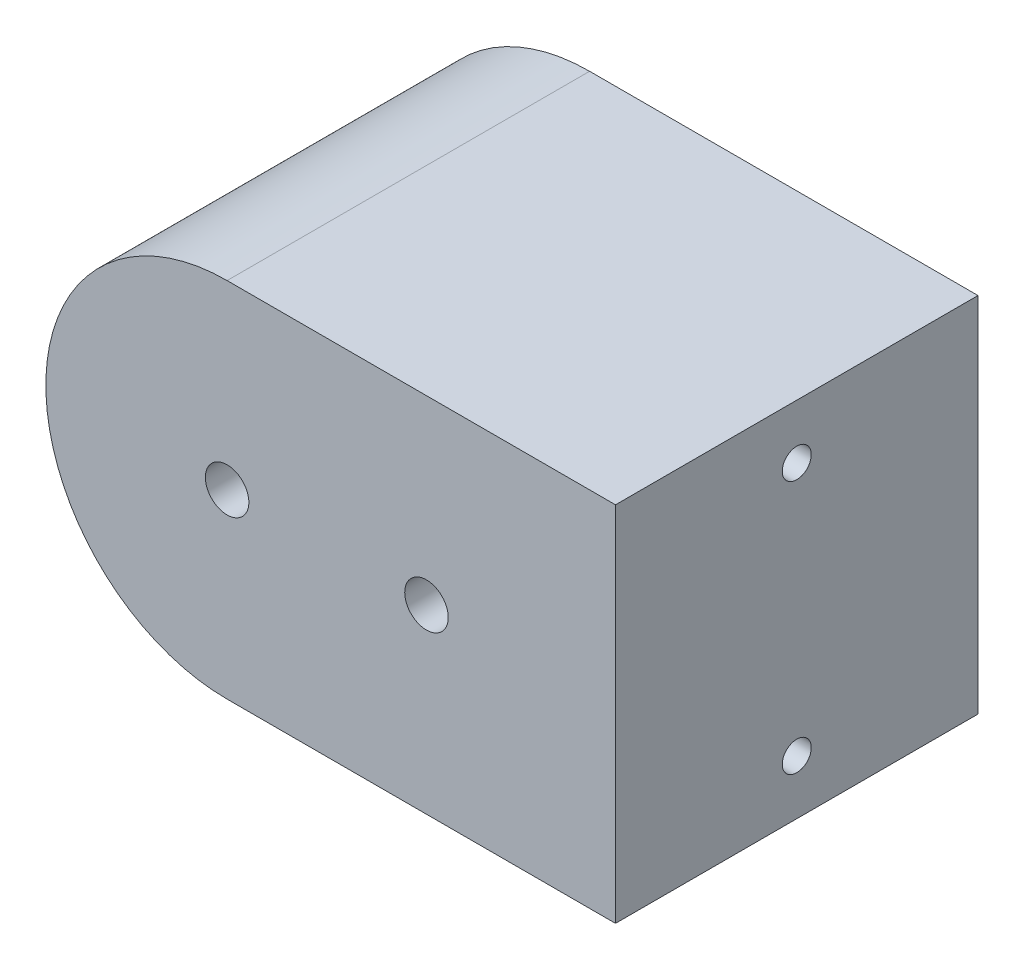
SolidWorks part; units mm, degrees
ref_plane "Front Plane" through (0, 0, 0) normal (0, 0, 1) x (1, 0, 0)
ref_plane "Top Plane" through (0, 0, 0) normal (0, 1, 0) x (1, 0, 0)
ref_plane "Right Plane" through (0, 0, 0) normal (1, 0, 0) x (0, 0, -1)
sketch "Sketch1" plane through (0, 0, 0) normal (0, 0, 1) x (1, 0, 0)
  line L1 (0, 0) -> (-75, 0)
  line L2 (0, 0) -> (0, 70)
  line L3 (0, 70) -> (-75, 70)
  arc A0 (-75, 0) -> (-75, 70) centre (-75, 35) cw
  point P6 (-36.5, 35)
  point P7 (0, 0)
  point P8 (0, 0)
  dimension "D3" = 75
  dimension "D4" = 35
  dimension "D1" = 70
  dimension "D2" = 75
  dimension "D5" = 38.5
extrude "Boss-Extrude1" add sketch "Sketch1" along normal blind 70
scale "Scale1" scale about centroid uniform scaling yes scale factor 1.428571
sketch "Sketch5" plane through (0, 0, -15) normal (0, 0, -1) x (-1, 0, 0)
  line L0 (85.0534, 85) -> (85.0534, -15) construction
  point P4 (85.0534, 35)
  point P5 (30.0534, 35)
  point P7 (0, 0)
  dimension "D1" = 55
hole_wizard "Ø12.0mm Dowel Hole1" positions "3DSketch1" profile "Sketch7" hole size "Ø12.0" standard "ISO" end condition through all
sketch3d "3DSketch1"
  point P0 (-30.0534, 35, -15)
  point P3 (-85.0534, 35, -15)
sketch "Sketch7" plane through (-30.0534, 35, -15) normal (1, 0, 0) x (0, 1, 0)
  line L0 (0, 0) -> (0, 100)
  line L1 (0, 100) -> (6, 100)
  line L2 (6, 100) -> (6, 0)
  line L5 (6, 0) -> (0, 0)
  line L11 (0, -6.35) -> (0, 107.95) construction
  dimension "Thru Hole Dia." = 12
  dimension "Thru Hole Depth" = 100
sketch "Sketch8" plane through (22.0895, 0, 0) normal (1, 0, 0) x (0, 0, -1)
  line L0 (-85, 70) -> (15, 70) construction
  line L1 (-85, -15) -> (-85, 85) construction
  line L2 (15, -15) -> (15, 85) construction
  line L3 (-85, 0) -> (15, 0) construction
  line L4 (-85, 85) -> (15, 85) construction
  line L5 (-85, -15) -> (15, -15) construction
  point P12 (-35, 70)
  point P13 (-35, 0)
  dimension "D1" = 15
  dimension "D2" = 15
hole_wizard "Ø8.0mm Dowel Hole3" positions "Sketch11" profile "Sketch12" hole size "Ø8.0" standard "ISO"
sketch "Sketch11" plane through (22.0895, 0, 0) normal (1, 0, 0) x (0, 0, -1)
  line L0 (-85, 70) -> (15, 70) construction
  point P0 (-35, 70)
  point P4 (-35, 0)
sketch "Sketch12" plane through (22.0895, 70, 35) normal (0, 1, 0) x (0, 0, -1)
  line L0 (0, 0) -> (0, 22.4034)
  line L1 (0, 22.4034) -> (4, 20)
  line L2 (4, 20) -> (4, 0)
  line L5 (4, 0) -> (0, 0)
  line L10 (0, 22.4034) -> (-4, 20) construction
  line L11 (0, -6.35) -> (0, 107.95) construction
  dimension "Hole Dia." = 8
  dimension "Hole Depth" = 20
  dimension "Drill Angle" = 118
